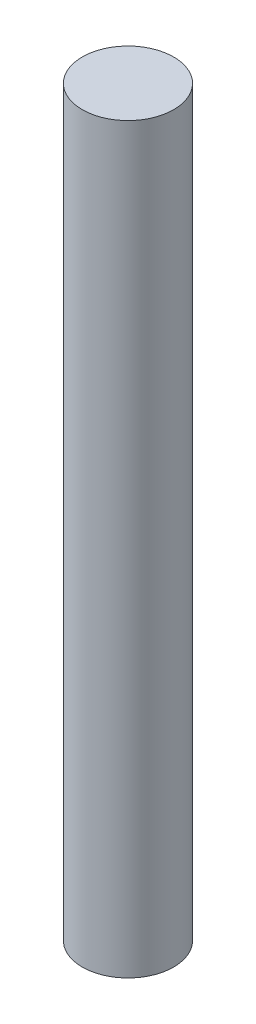
SolidWorks part; units mm, degrees
ref_plane "Front Plane" through (0, 0, 0) normal (0, 0, 1) x (1, 0, 0)
ref_plane "Top Plane" through (0, 0, 0) normal (0, 1, 0) x (1, 0, 0)
ref_plane "Right Plane" through (0, 0, 0) normal (1, 0, 0) x (0, 0, -1)
sketch "Sketch1" plane through (0, 0, 0) normal (0, 1, 0) x (1, 0, 0)
  circle A0 centre (0, 0) radius 4
extrude "Boss-Extrude1" add sketch "Sketch1" along normal blind 65
